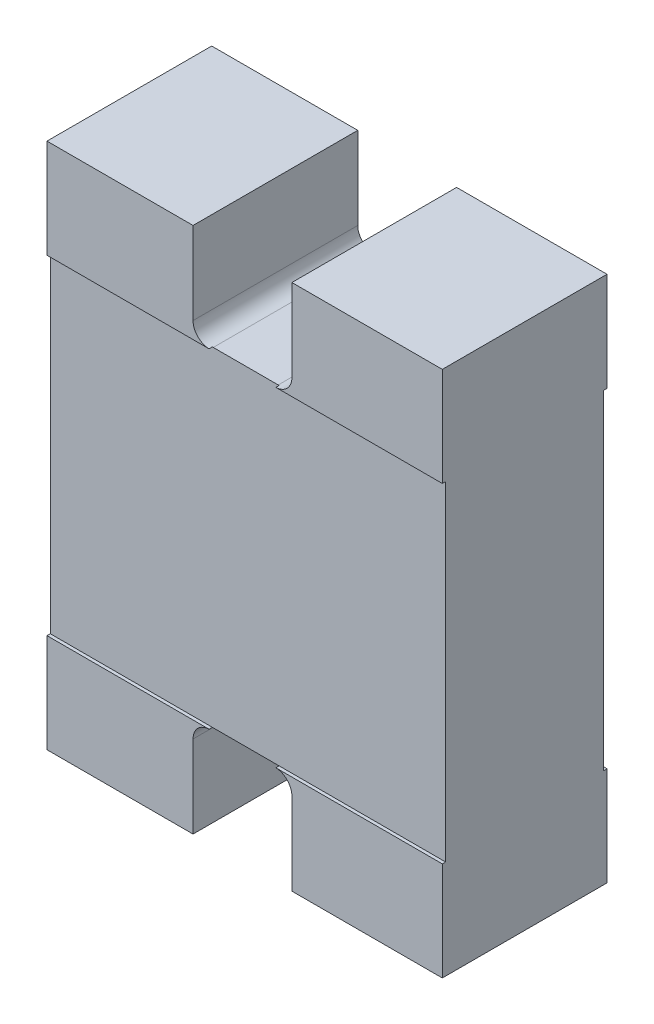
SolidWorks part; units mm, degrees
ref_plane "Front Plane" through (0, 0, 0) normal (0, 0, 1) x (1, 0, 0)
ref_plane "Top Plane" through (0, 0, 0) normal (0, 1, 0) x (1, 0, 0)
ref_plane "Right Plane" through (0, 0, 0) normal (1, 0, 0) x (0, 0, -1)
sketch "Sketch1" plane through (0, 0, 0) normal (0, 0, 1) x (1, 0, 0)
  line L1 (-0.6, 0.8) -> (0.6, 0.8)
  line L2 (-0.6, 0.8) -> (-0.6, -0.8)
  line L3 (-0.6, -0.8) -> (0.6, -0.8)
  line L4 (0.6, 0.8) -> (0.6, -0.8)
  line L5 (-0.6, 0.8) -> (0.6, -0.8) construction
  line L6 (-0.6, -0.8) -> (0.6, 0.8) construction
  point P0 (0, 0)
  dimension "D1" = 1.2
  dimension "D2" = 1.6
extrude "Boss-Extrude1" add sketch "Sketch1" along normal blind 0.5
sketch "Sketch2" plane through (0, 0, 0) normal (0, 0, -1) x (-1, 0, 0)
  line L0 (0, 0.8) -> (0, -0.8) construction
  line L1 (-0.6, 0.8) -> (0.6, 0.8) construction
  line L2 (0.6, -0.8) -> (-0.6, -0.8) construction
  line L3 (-0.6, 0) -> (0.6, 0) construction
  line L4 (-0.6, -0.8) -> (-0.6, 0.8) construction
  line L5 (0.6, 0.8) -> (0.6, -0.8) construction
  line L6 (-0.4, 0.8) -> (-0.4, -0.8) construction
  line L7 (-0.6, 0.5) -> (0.6, 0.5) construction
  line L8 (-0.1434, 0.55) -> (0.1566, 0.55) construction
  line L9 (0.1566, 0.8) -> (0.1566, 0.55)
  line L13 (-0.1434, 0.8) -> (-0.1434, 0.55)
  line L17 (-0.092, 0.5) -> (0.1052, 0.5)
  line L19 (-0.1434, 0.8) -> (0.1566, 0.8)
  arc A0 (0.1566, 0.55) -> (0.1052, 0.5) centre (0.1066, 0.55) cw
  arc A3 (-0.1434, 0.55) -> (-0.092, 0.5) centre (-0.0934, 0.55) ccw
  point P18 (-0.1138, 0.8)
  point P21 (-0.1434, 0.8)
  point P22 (0.1415, 0.5141)
  point P50 (0, 0.5)
  dimension "D4" = 0.05
  dimension "D8" = 0.05
  dimension "D1" = 0.4
  dimension "D2" = 0.3
  dimension "D3" = 0.3
  dimension "D6" = 0.1972
extrude "Cut-Extrude1" cut sketch "Sketch2" against normal through all
sketch "Sketch3" plane through (0, 0, 0) normal (0, 0, -1) x (-1, 0, 0)
  line L0 (-0.6, 0.5) -> (0.6, 0.5) construction
  line L1 (-0.6, -0.8) -> (-0.6, 0.8) construction
  line L2 (0.6, 0.8) -> (0.6, -0.8) construction
  line L3 (-0.6, -0.5) -> (0.6, -0.5) construction
  line L5 (-0.6, 0.5) -> (0.6, 0.5)
  line L6 (-0.6, 0.5) -> (-0.6, -0.5)
  line L7 (-0.6, -0.5) -> (0.6, -0.5)
  line L8 (0.6, 0.5) -> (0.6, -0.5)
extrude "Cut-Extrude2" cut sketch "Sketch3" against normal blind 0.01
ref_plane "Plane1" through (0, 0, 0.25) normal (0, 0, -1) x (-1, 0, 0)
mirror "Mirror0" about plane through (0, 0, 0) normal (0, 1, 0) of "Cut-Extrude1"
mirror "Mirror1" about plane through (0, 0, 0.25) normal (0, 0, -1) of "Cut-Extrude2"
mirror "Mirror3" [suppressed] about plane through (0, 0, 0) normal (1, 0, 0)
sketch "Sketch5" plane through (0, 0, 0.01) normal (0, 0, -1) x (-1, 0, 0)
  line L0 (-0.6, -0.1976) -> (0.6, -0.1976) construction
  line L1 (-0.6, 0.5) -> (-0.6, -0.5) construction
  line L2 (0.6, -0.5) -> (0.6, 0.5) construction
  text T0 "<b>EXB38V  </b>" font "Tahoma" height 0.5
extrude "Boss-Extrude3" [suppressed] add sketch "Sketch5" along normal blind 0.01
